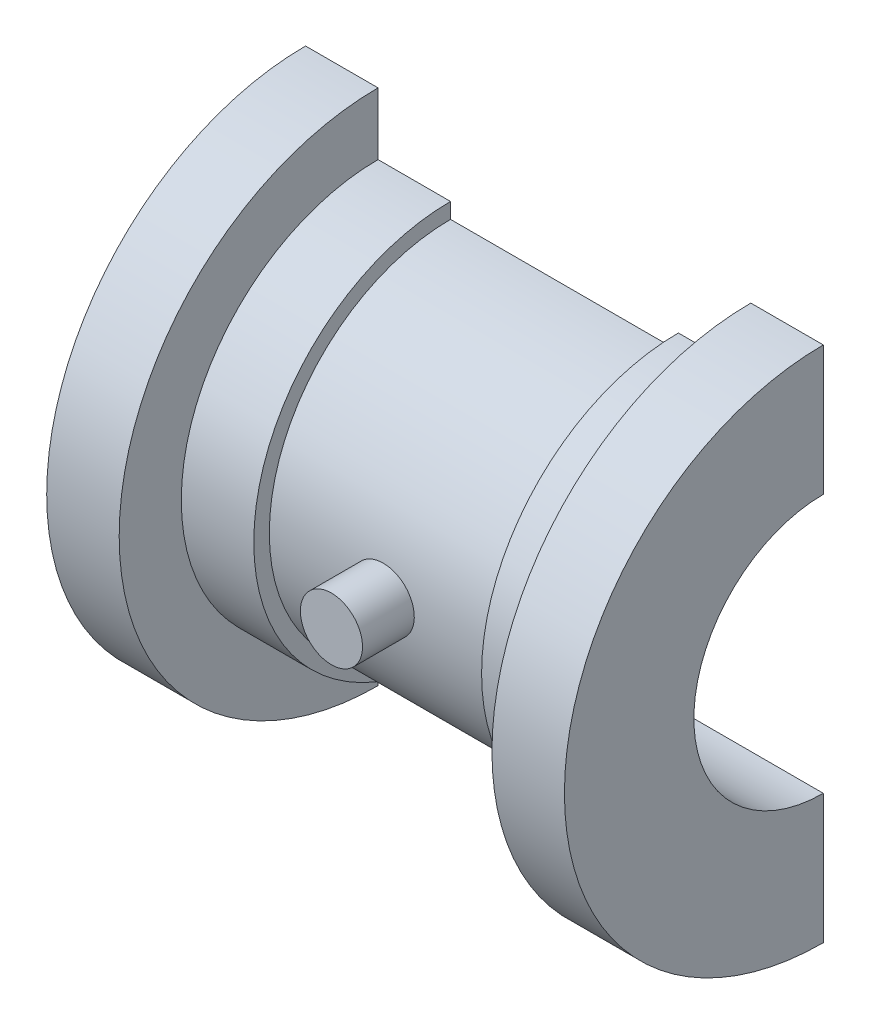
SolidWorks part; units mm, degrees
ref_plane "Front Plane" through (0, 0, 0) normal (0, 0, 1) x (1, 0, 0)
ref_plane "Top Plane" through (0, 0, 0) normal (0, 1, 0) x (1, 0, 0)
ref_plane "Right Plane" through (0, 0, 0) normal (1, 0, 0) x (0, 0, -1)
sketch "Sketch1" plane through (0, 0, 0) normal (0, 0, 1) x (1, 0, 0)
  line L0 (-38.9494, 0) -> (38.9494, 0) construction
  line L1 (0, 19.9347) -> (0, 17.5) construction
  line L2 (25, 0) -> (-25, 0)
  line L3 (-25, 0) -> (-25, 25)
  line L4 (-25, 25) -> (-18, 25)
  line L5 (-18, 25) -> (-18, 19)
  line L6 (-18, 19) -> (-11, 19)
  line L7 (-11, 19) -> (-11, 17.5)
  line L8 (-11, 17.5) -> (11, 17.5)
  line L10 (11, 19) -> (11, 17.5)
  line L11 (18, 19) -> (11, 19)
  line L12 (18, 25) -> (18, 19)
  line L13 (25, 25) -> (18, 25)
  line L14 (25, 0) -> (25, 25)
  line L15 (0, 0) -> (0, -19.9347) construction
  point P3 (0, 0)
  dimension "D1" = 25
  dimension "D2" = 25
  dimension "D5" = 19
  dimension "D6" = 17.5
revolve "Revolve1" add sketch "Sketch1" angle 180 about L0
sketch "Sketch2" plane through (-25, 0, 0) normal (-1, 0, 0) x (0, 0, 1)
  line L0 (0, -25) -> (0, 25) construction
  line L1 (0, 12.5) -> (0, -12.5)
  arc A0 (0, -12.5) -> (0, 12.5) centre (0, 0) ccw
extrude "Cut-Extrude3" cut sketch "Sketch2" against normal blind 50
ref_plane "Plane2" through (0, 0, 17.5) normal (0, 0, -1) x (-1, 0, 0)
sketch "Sketch4" plane through (0, 0, 17.5) normal (0, 0, -1) x (-1, 0, 0)
  circle A0 centre (0, 0) radius 3
  dimension "D1" = 6
extrude "Boss-Extrude1" add sketch "Sketch4" against normal blind 5 separate body contours A0
